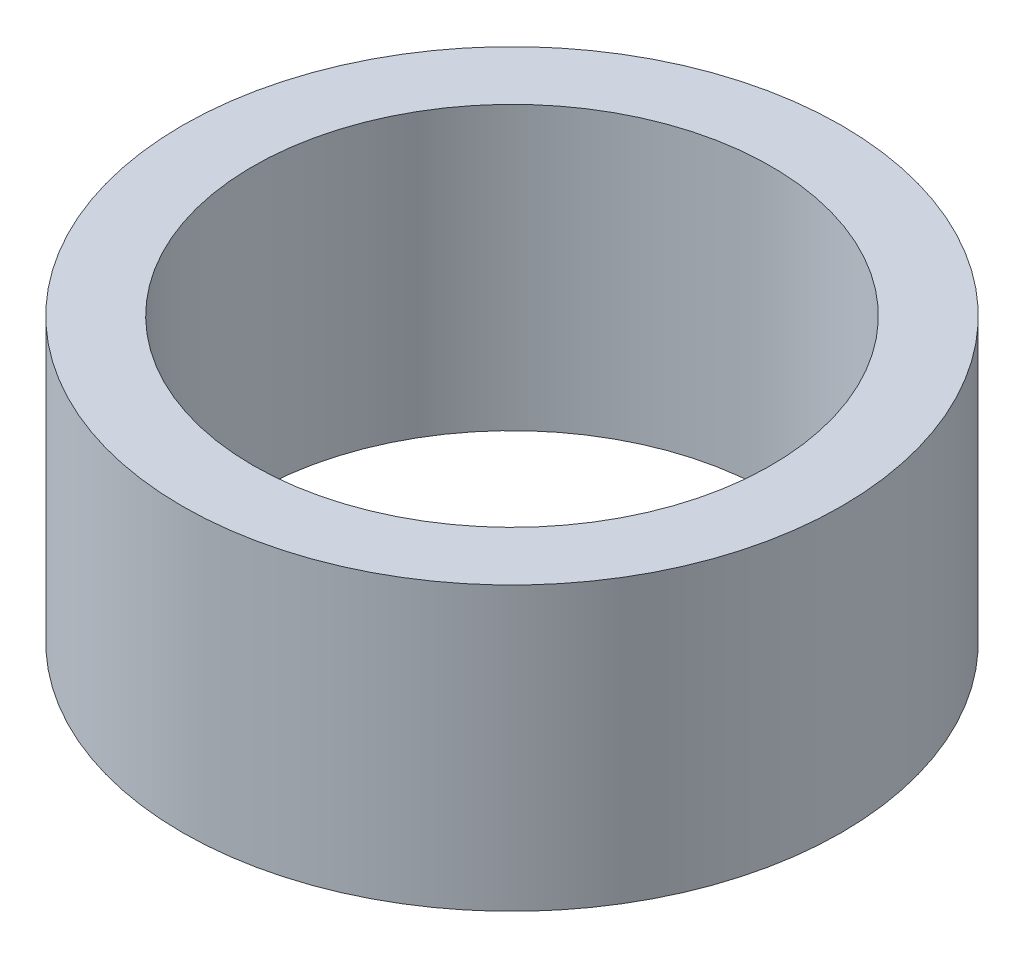
SolidWorks part; units mm, degrees
ref_plane "Front Plane" through (0, 0, 0) normal (0, 0, 1) x (1, 0, 0)
ref_plane "Top Plane" through (0, 0, 0) normal (0, 1, 0) x (1, 0, 0)
ref_plane "Right Plane" through (0, 0, 0) normal (1, 0, 0) x (0, 0, -1)
sketch "Sketch2" plane through (0, 0, 0) normal (0, 1, 0) x (1, 0, 0)
  circle A0 centre (0, 0) radius 11
  circle A1 centre (0, 0) radius 14
  dimension "D1" = 22
  dimension "D2" = 3
extrude "Boss-Extrude1" add sketch "Sketch2" along normal blind 12
equation "\"m3 hole\"= 3.2"
equation "\"m4 hole\"= 4.2"
equation "\"m5 hole\"= 5.2"
equation "\"m6 hole\"= 6.2"
equation "\"m8 hole\"= 8.2"
equation "\"m3 tapped\"= 2.5"
equation "\"m4 tapped\"= 3.3"
equation "\"m5 tapped\"= 4.2"
equation "\"m6 tapped\"= 5"
equation "\"m8 tapped\"= 6.8"
